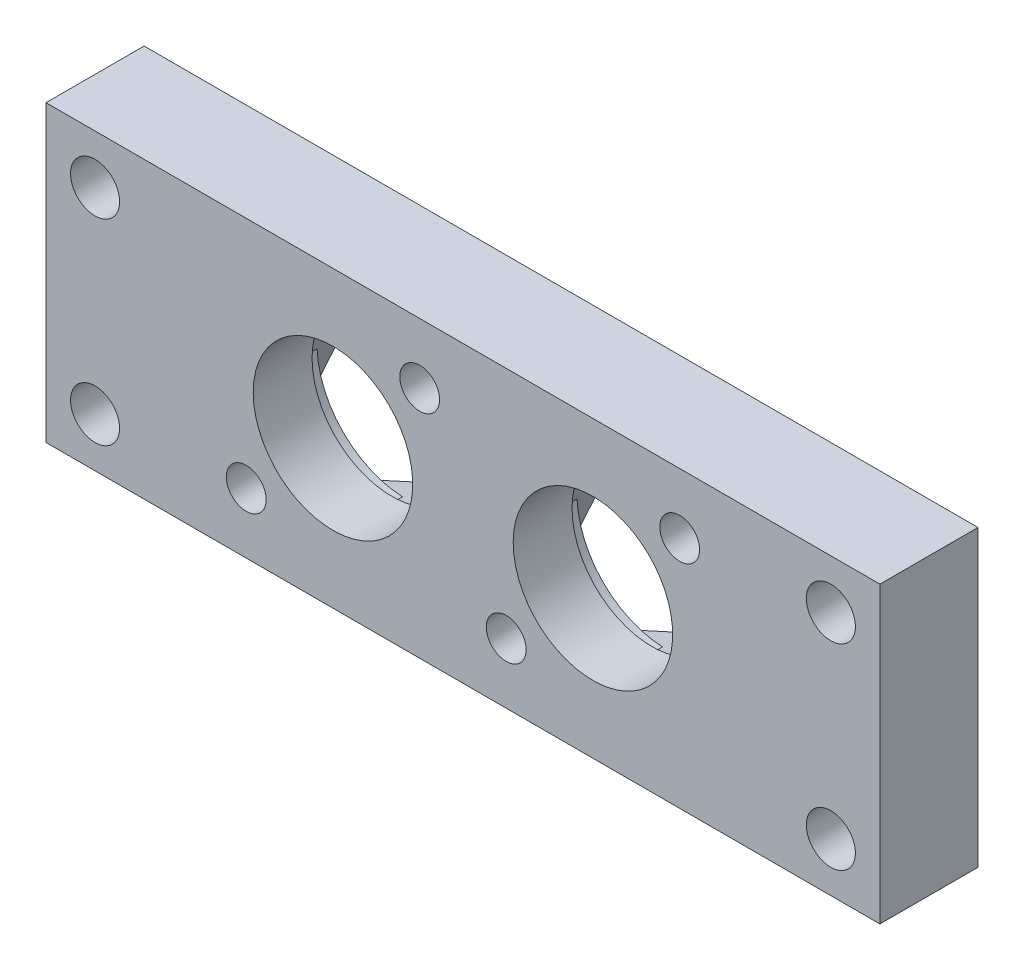
SolidWorks part; units mm, degrees
ref_plane "Front Plane" through (0, 0, 0) normal (0, 0, 1) x (1, 0, 0)
ref_plane "Top Plane" through (0, 0, 0) normal (0, 1, 0) x (1, 0, 0)
ref_plane "Right Plane" through (0, 0, 0) normal (1, 0, 0) x (0, 0, -1)
sketch "Sketch1" plane through (0, 0, 0) normal (0, 0, 1) x (1, 0, 0)
  line L0 (-33.655, 0) -> (33.655, 0) construction
  line L1 (-56.1056, -22.4506) -> (-11.2044, 22.4506) construction
  line L2 (107.95, -38.1) -> (-107.95, -38.1)
  line L3 (107.95, -38.1) -> (107.95, 38.1)
  line L4 (107.95, 38.1) -> (-107.95, 38.1)
  line L5 (-107.95, -38.1) -> (-107.95, 38.1)
  line L6 (107.95, -38.1) -> (-107.95, 38.1) construction
  line L7 (107.95, 38.1) -> (-107.95, -38.1) construction
  line L8 (-64.7837, -18.4935) -> (-52.444, 8.5677)
  line L9 (-52.1485, -31.1287) -> (-25.0873, -18.789)
  line L10 (-42.2227, 18.789) -> (-15.1615, 31.1287)
  line L11 (-14.866, -8.5677) -> (-2.5263, 18.4935)
  line L12 (52.444, -8.5677) -> (64.7837, 18.4935)
  line L13 (25.0873, 18.789) -> (52.1485, 31.1287)
  line L14 (2.5263, -18.4935) -> (14.866, 8.5677)
  line L15 (11.2044, -22.4506) -> (56.1056, 22.4506) construction
  line L16 (15.1615, -31.1287) -> (42.2227, -18.789)
  circle A0 centre (-33.655, 0) radius 20.6502
  circle A2 centre (-11.2044, 22.4506) radius 5.1594
  circle A3 centre (-56.1056, -22.4506) radius 5.1594
  circle A4 centre (-11.2044, 22.4506) radius 9.5377
  circle A5 centre (-56.1056, -22.4506) radius 9.5377
  circle A6 centre (-33.655, 0) radius 6.3627
  circle A7 centre (56.1056, 22.4506) radius 9.5377
  circle A8 centre (56.1056, 22.4506) radius 5.1594
  circle A9 centre (33.655, 0) radius 20.6502
  circle A10 centre (11.2044, -22.4506) radius 9.5377
  circle A11 centre (11.2044, -22.4506) radius 5.1594
  circle A12 centre (33.655, 0) radius 6.3627
  point P4 (0, 0)
  point P5 (0, 0)
  point P11 (-33.655, 0)
  dimension "D2" = 41.3004
  dimension "D3" = 10.3187
  dimension "D4" = 82.5754
  dimension "D7" = 12.7254
  dimension "D1" = 67.31
  dimension "D5" = 63.5
  dimension "D6" = 45
  dimension "D8" = 215.9
  dimension "D9" = 76.2
  dimension "D10" = 2
  dimension "D11" = 2
extrude "Boss-Extrude1" add sketch "Sketch1" along normal mid plane 25.4 contours L5 L2 L3 L4 A10 L14 A9 L13 A7 L12 L16 A5 L8 A0 L10 A4 L11 L9
sketch "Sketch2" plane through (0, 0, 12.7) normal (0, 0, 1) x (1, 0, 0)
  line L0 (-64.7837, -18.4935) -> (-52.444, 8.5677) construction
  line L1 (-52.1485, -31.1287) -> (-25.0873, -18.789) construction
  line L2 (-14.866, -8.5677) -> (-2.5263, 18.4935) construction
  line L3 (-42.2227, 18.789) -> (-15.1615, 31.1287) construction
  line L4 (-64.7837, -18.4935) -> (-52.444, 8.5677)
  line L5 (-52.1485, -31.1287) -> (-25.0873, -18.789)
  line L6 (-14.866, -8.5677) -> (-2.5263, 18.4935)
  line L7 (-42.2227, 18.789) -> (-15.1615, 31.1287)
  arc A0 (-42.2227, 18.789) -> (-52.444, 8.5677) centre (-33.655, 0) ccw construction
  arc A1 (-64.7837, -18.4935) -> (-52.1485, -31.1287) centre (-56.1056, -22.4506) ccw construction
  arc A2 (-25.0873, -18.789) -> (-14.866, -8.5677) centre (-33.655, 0) ccw construction
  arc A3 (-2.5263, 18.4935) -> (-15.1615, 31.1287) centre (-11.2044, 22.4506) ccw construction
  arc A4 (-42.2227, 18.789) -> (-52.444, 8.5677) centre (-33.655, 0) ccw
  arc A5 (-64.7837, -18.4935) -> (-52.1485, -31.1287) centre (-56.1056, -22.4506) ccw
  arc A6 (-25.0873, -18.789) -> (-14.866, -8.5677) centre (-33.655, 0) ccw
  arc A7 (-2.5263, 18.4935) -> (-15.1615, 31.1287) centre (-11.2044, 22.4506) ccw
  circle A8 centre (-11.2044, 22.4506) radius 5.1594
  circle A9 centre (-56.1056, -22.4506) radius 5.1594
  circle A10 centre (-33.655, 0) radius 6.985
  dimension "D1" = 10.3187
  dimension "D2" = 10.3187
  dimension "D3" = 13.97
extrude "Boss-Extrude2" add sketch "Sketch2" against normal offset from surface (9.525 mm away) 15.875 up to face at (33.655, 0, -12.7)
sketch "Sketch3" plane through (0, 0, 3.175) normal (0, 0, -1) x (-1, 0, 0)
  line L4 (42.2227, 18.789) -> (15.1615, 31.1287)
  line L5 (2.5263, 18.4935) -> (14.866, -8.5677)
  line L6 (25.0873, -18.789) -> (52.1485, -31.1287)
  line L7 (64.7837, -18.4935) -> (52.444, 8.5677)
  line L8 (42.2227, 18.789) -> (15.1615, 31.1287)
  line L9 (2.5263, 18.4935) -> (14.866, -8.5677)
  line L10 (25.0873, -18.789) -> (52.1485, -31.1287)
  line L11 (64.7837, -18.4935) -> (52.444, 8.5677)
  circle A0 centre (33.655, 0) radius 20.6502
  arc A4 (52.444, 8.5677) -> (42.2227, 18.789) centre (33.655, 0) ccw
  arc A5 (15.1615, 31.1287) -> (2.5263, 18.4935) centre (11.2044, 22.4506) ccw
  arc A6 (14.866, -8.5677) -> (25.0873, -18.789) centre (33.655, 0) ccw
  arc A7 (52.1485, -31.1287) -> (64.7837, -18.4935) centre (56.1056, -22.4506) ccw
  arc A8 (52.444, 8.5677) -> (42.2227, 18.789) centre (33.655, 0) ccw
  arc A9 (15.1615, 31.1287) -> (2.5263, 18.4935) centre (11.2044, 22.4506) ccw
  arc A10 (14.866, -8.5677) -> (25.0873, -18.789) centre (33.655, 0) ccw
  arc A11 (52.1485, -31.1287) -> (64.7837, -18.4935) centre (56.1056, -22.4506) ccw
  line M11 (42.2227, 18.789) -> (15.1615, 31.1287)
  arc M12 (15.1615, 31.1287) -> (2.5263, 18.4935) centre (11.2044, 22.4506) ccw
  line M13 (2.5263, 18.4935) -> (14.866, -8.5677)
  line M15 (25.0873, -18.789) -> (52.1485, -31.1287)
  arc M16 (52.1485, -31.1287) -> (64.7837, -18.4935) centre (56.1056, -22.4506) ccw
  line M17 (64.7837, -18.4935) -> (52.444, 8.5677)
  circle M18 centre (56.1056, -22.4506) radius 5.1594
  circle M20 centre (11.2044, 22.4506) radius 5.1594
  dimension "D1" = 0
extrude "Boss-Extrude3" add sketch "Sketch3" along normal offset from surface (9.525 mm away) 6.35 contours A0 M11 M12 M13 M20 | A0 M15 M16 M17 M18 up to face at (33.655, 0, -12.7)
sketch "Sketch4" plane through (0, 0, -6.35) normal (0, 0, -1) x (-1, 0, 0)
  line L0 (52.1485, -31.1287) -> (25.0873, -18.789) construction
  line L1 (64.7837, -18.4935) -> (52.444, 8.5677) construction
  line L2 (14.866, -8.5677) -> (2.5263, 18.4935) construction
  line L3 (42.2227, 18.789) -> (15.1615, 31.1287) construction
  line L4 (34.6887, -23.1671) -> (25.0873, -18.789)
  line L5 (56.8221, -1.0337) -> (52.444, 8.5677)
  line L6 (14.866, -8.5677) -> (10.4879, 1.0337)
  line L7 (42.2227, 18.789) -> (32.6213, 23.1671)
  circle A0 centre (33.655, 0) radius 23.1902
  circle A1 centre (33.655, 0) radius 20.6502 construction
  circle A2 centre (33.655, 0) radius 20.6502
  arc A3 (52.444, 8.5677) -> (42.2227, 18.789) centre (33.655, 0) ccw construction
  arc M3 (14.866, -8.5677) -> (42.2227, 18.789) centre (33.655, 0) cw
  line M4 (42.2227, 18.789) -> (15.1615, 31.1287)
  line M6 (2.5263, 18.4935) -> (14.866, -8.5677)
  dimension "D1" = 2.54
extrude "Cut-Extrude1" cut sketch "Sketch4" against normal blind 3.81 contours A0 M4 M6 M3 | A2 L4 A0 L5
pattern_linear "LPattern1" count 2 spacing 67.31 along (1, 0, 0) of "Boss-Extrude3", "Boss-Extrude2", "Cut-Extrude1"
sketch "Sketch5" plane through (0, 0, 3.175) normal (0, 0, -1) x (-1, 0, 0)
  circle A0 centre (33.655, 0) radius 13.335
  circle A1 centre (-33.655, 0) radius 13.335
  dimension "D1" = 26.67
extrude "Cut-Extrude2" cut sketch "Sketch5" against normal blind 2.54
sketch "Sketch6" plane through (0, 0, -12.7) normal (0, 0, -1) x (-1, 0, 0)
  line L0 (-107.95, -38.1) -> (-107.95, 38.1) construction
  line L1 (-107.95, 38.1) -> (107.95, 38.1) construction
  line L2 (-107.95, -38.1) -> (107.95, -38.1) construction
  line L3 (0, 38.1) -> (0, -38.1) construction
  circle A0 centre (-95.25, 25.4) radius 6.35
  circle A1 centre (-95.25, -25.4) radius 6.35
  circle A2 centre (95.25, -25.4) radius 6.35
  circle A3 centre (95.25, 25.4) radius 6.35
  dimension "D3" = 12.7
  dimension "D4" = 12.7
  dimension "D1" = 12.7
  dimension "D2" = 12.7
  dimension "D5" = 12.7
extrude "Cut-Extrude3" cut sketch "Sketch6" against normal through all
sketch "Sketch7" plane through (0, 0, 3.175) normal (0, 0, -1) x (-1, 0, 0)
  circle A0 centre (-33.655, 0) radius 20.6502
  circle A1 centre (33.655, 0) radius 20.6502
  arc A2 (-25.0873, 18.789) -> (-52.444, -8.5677) centre (-33.655, 0) ccw construction
  circle A3 centre (33.655, 0) radius 20.6502 construction
extrude "Cut-Extrude4" cut sketch "Sketch7" against normal through all
